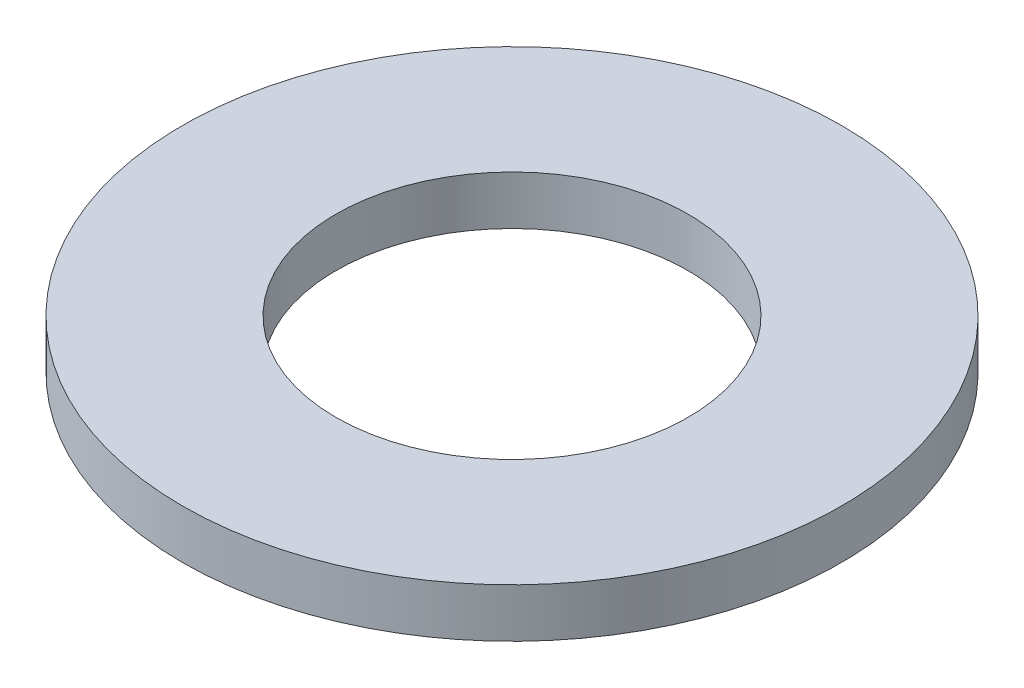
SolidWorks part; units mm, degrees
ref_plane "Front Plane" through (0, 0, 0) normal (0, 0, 1) x (1, 0, 0)
ref_plane "Top Plane" through (0, 0, 0) normal (0, 1, 0) x (1, 0, 0)
ref_plane "Right Plane" through (0, 0, 0) normal (1, 0, 0) x (0, 0, -1)
sketch "Sketch1" plane through (0, 0, 0) normal (0, 1, 0) x (1, 0, 0)
  circle A0 centre (0, 0) radius 22.225
  dimension "OD" = 44.45
extrude "Boss-Extrude1" add sketch "Sketch1" along normal blind 3.302
sketch "Sketch5" plane through (0, 3.302, 0) normal (0, 1, 0) x (-1, 0, 0)
  circle A0 centre (0, 0) radius 11.8745
  dimension "ID" = 23.749
extrude "Cut-Extrude1" cut sketch "Sketch5" against normal through all
